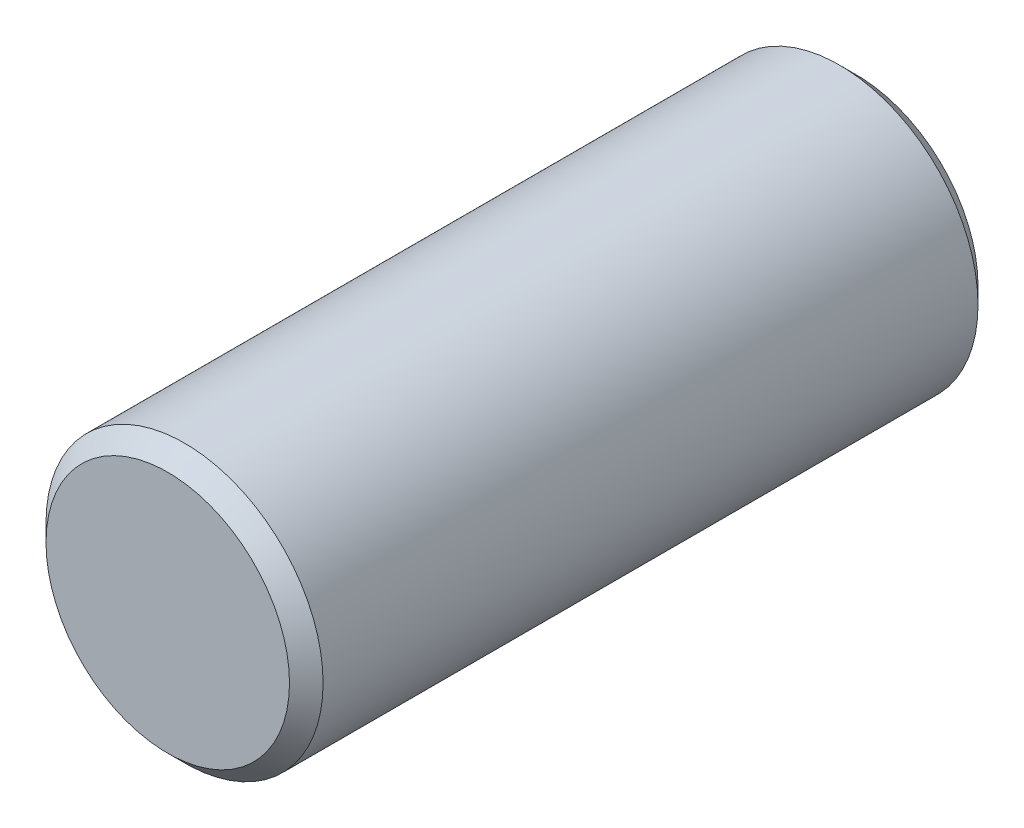
SolidWorks part; units mm, degrees
ref_plane "Front Plane" through (0, 0, 0) normal (0, 0, 1) x (1, 0, 0)
ref_plane "Top Plane" through (0, 0, 0) normal (0, 1, 0) x (1, 0, 0)
ref_plane "Right Plane" through (0, 0, 0) normal (1, 0, 0) x (0, 0, -1)
sketch "Sketch1" plane through (0, 0, 0) normal (0, 0, 1) x (1, 0, 0)
  circle A0 centre (0, 0) radius 16.5
  dimension "D1" = 33
extrude "Boss-Extrude1" add sketch "Sketch1" along normal mid plane 82
chamfer "Chamfer1" distance 2 angle 45 2 edges at (16.5, 0, -41) (16.5, 0, 41)
